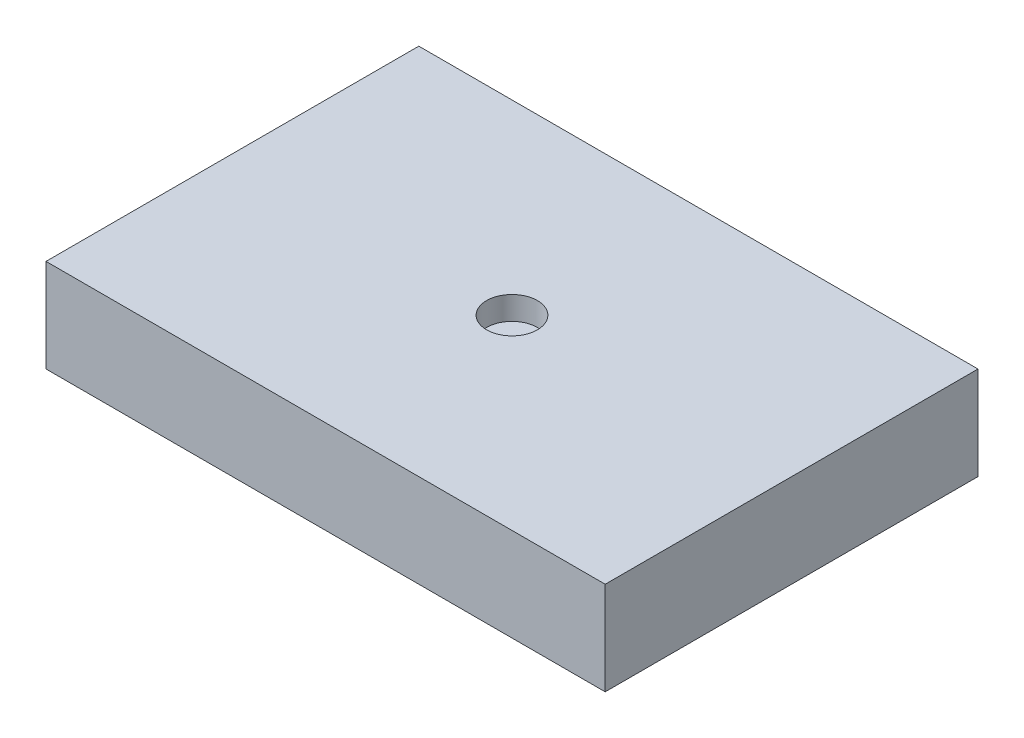
SolidWorks part; units mm, degrees
ref_plane "Front Plane" through (0, 0, 0) normal (0, 0, 1) x (1, 0, 0)
ref_plane "Top Plane" through (0, 0, 0) normal (0, 1, 0) x (1, 0, 0)
ref_plane "Right Plane" through (0, 0, 0) normal (1, 0, 0) x (0, 0, -1)
sketch "Sketch1" plane through (0, 0, 0) normal (0, 1, 0) x (1, 0, 0)
  line L1 (-15.24, -10.16) -> (15.24, -10.16)
  line L2 (-15.24, -10.16) -> (-15.24, 10.16)
  line L3 (-15.24, 10.16) -> (15.24, 10.16)
  line L4 (15.24, -10.16) -> (15.24, 10.16)
  line L5 (-15.24, -10.16) -> (15.24, 10.16) construction
  line L6 (-15.24, 10.16) -> (15.24, -10.16) construction
  point P0 (0, 0)
  dimension "D1" = 20.32
  dimension "D2" = 30.48
extrude "Boss-Extrude1" add sketch "Sketch1" along normal blind 5.08
sketch "Sketch2" plane through (0, 5.08, 0) normal (0, 1, 0) x (1, 0, 0)
  circle A0 centre (0, 0) radius 1.3839
extrude "Cut-Extrude1" cut sketch "Sketch2" against normal blind 1.27
